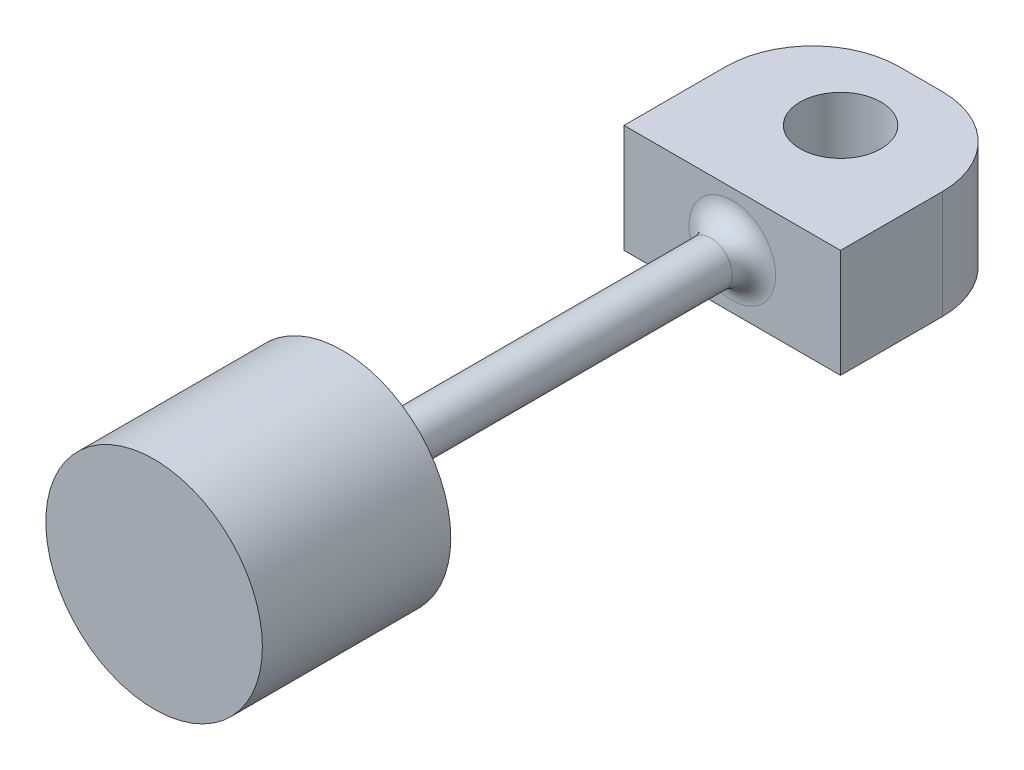
SolidWorks part; units mm, degrees
material "Plain Carbon Steel"
ref_plane "Front Plane" through (0, 0, 0) normal (0, 0, 1) x (1, 0, 0)
ref_plane "Top Plane" through (0, 0, 0) normal (0, 1, 0) x (1, 0, 0)
ref_plane "Right Plane" through (0, 0, 0) normal (1, 0, 0) x (0, 0, -1)
sketch "Sketch1" plane through (0, 0, 0) normal (0, 0, 1) x (1, 0, 0)
  circle A0 centre (0, 0) radius 6.35
  dimension "D1" = 12.7
extrude "Boss-Extrude1" add sketch "Sketch1" against normal blind 11.049
sketch "Sketch2" plane through (0, 0, -11.049) normal (0, 0, -1) x (-1, 0, 0)
  circle A0 centre (0, 0) radius 1.27
  dimension "D1" = 2.54
extrude "Boss-Extrude2" add sketch "Sketch2" along normal blind 22.86
fillet "Fillet1" radius 1.27 1 edges at (-1.27, 0, -11.049)
sketch "Sketch3" plane through (0, 0, -33.909) normal (0, 0, -1) x (-1, 0, 0)
  line L1 (6.35, -3.175) -> (-6.35, -3.175)
  line L2 (6.35, -3.175) -> (6.35, 3.175)
  line L3 (6.35, 3.175) -> (-6.35, 3.175)
  line L4 (-6.35, -3.175) -> (-6.35, 3.175)
  line L5 (6.35, -3.175) -> (-6.35, 3.175) construction
  line L6 (6.35, 3.175) -> (-6.35, -3.175) construction
  point P0 (0, 0)
  dimension "D1" = 6.35
  dimension "D2" = 12.7
extrude "Boss-Extrude3" add sketch "Sketch3" along normal blind 11.049
fillet "Fillet2" radius 1.27 1 edges at (-1.27, 0, -33.909)
fillet "Fillet3" radius 5.08 2 edges at (-6.35, 0, -44.958) (6.35, 0, -44.958)
sketch "Sketch4" plane through (0, 3.175, 0) normal (0, 1, 0) x (1, 0, 0)
  line L0 (-6.35, 33.909) -> (6.35, 33.909) construction
  line L1 (6.35, 39.878) -> (6.35, 33.909) construction
  circle A0 centre (0, 40.259) radius 2.3749
  dimension "D1" = 4.7498
  dimension "D2" = 6.35
  dimension "D3" = 6.35
extrude "Cut-Extrude1" cut sketch "Sketch4" against normal through all
